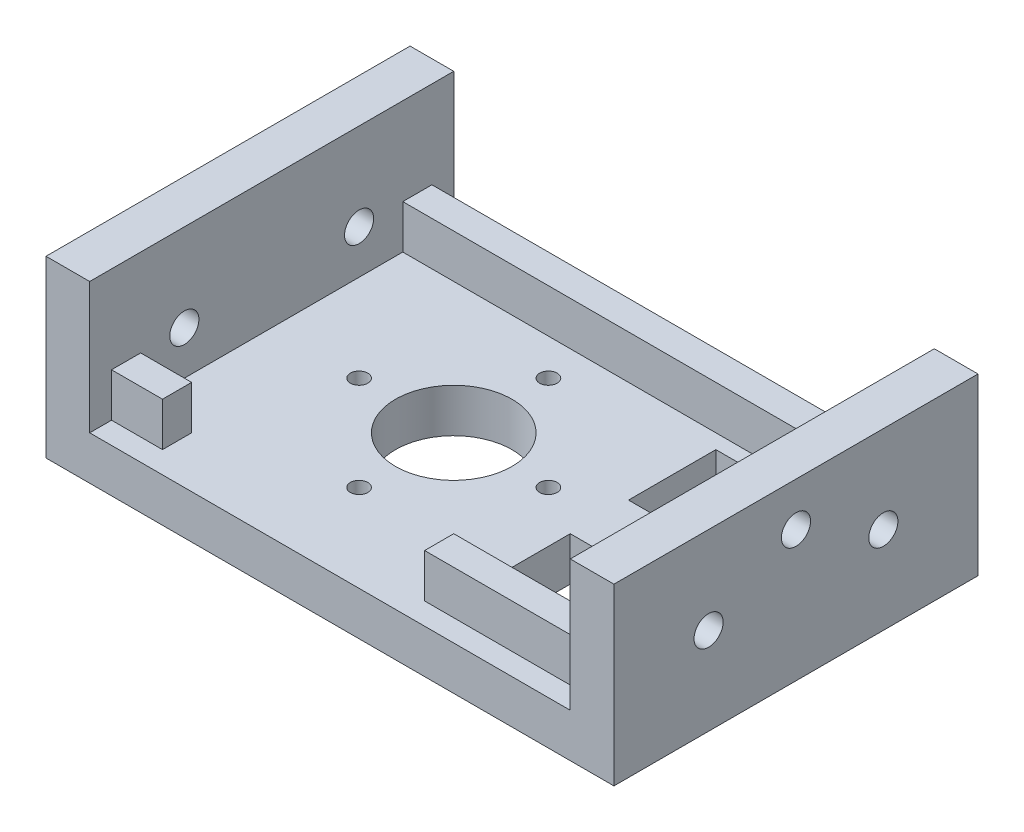
SolidWorks part; units mm, degrees
ref_plane "Alzado" through (0, 0, 0) normal (0, 0, 1) x (1, 0, 0)
ref_plane "Planta" through (0, 0, 0) normal (0, 1, 0) x (1, 0, 0)
ref_plane "Vista lateral" through (0, 0, 0) normal (1, 0, 0) x (0, 0, -1)
sketch "Croquis1" plane through (0, 0, 0) normal (0, 1, 0) x (1, 0, 0)
  line L0 (-18.5924, 13.748) -> (20.4076, 13.748)
  line L1 (-18.5924, 13.748) -> (-18.5924, -11.252)
  line L2 (-18.5924, -11.252) -> (20.4076, -11.252)
  line L3 (20.4076, 13.748) -> (20.4076, -11.252)
  line L4 (6.9076, -0.752) -> (14.9076, -0.752)
  line L5 (6.9076, -0.752) -> (6.9076, -6.752)
  line L6 (6.9076, -6.752) -> (14.9076, -6.752)
  line L7 (14.9076, -0.752) -> (14.9076, -6.752)
  line L8 (6.9076, 9.248) -> (14.9076, 9.248)
  line L9 (6.9076, 9.248) -> (6.9076, 3.248)
  line L10 (6.9076, 3.248) -> (14.9076, 3.248)
  line L11 (14.9076, 9.248) -> (14.9076, 3.248)
  circle A0 centre (-3.0924, 1.248) radius 4
  circle A1 centre (-3.0924, 7.748) radius 0.6
  circle A2 centre (3.4076, 1.248) radius 0.6
  circle A3 centre (-3.0924, -5.252) radius 0.6
  circle A4 centre (-9.5924, 1.248) radius 0.6
  point P22 (-3.0924, 1.248)
extrude "Saliente-Extruir1" add sketch "Croquis1" along normal blind 3
sketch "Croquis2" plane through (0, 3, 0) normal (0, 1, 0) x (1, 0, 0)
  line L0 (-18.5924, -11.252) -> (20.4076, -11.252) construction
  line L1 (-18.5924, 13.748) -> (-15.5924, 13.748)
  line L2 (-18.5924, 13.748) -> (-18.5924, -11.252)
  line L3 (-18.5924, -11.252) -> (-15.5924, -11.252)
  line L4 (-15.5924, 13.748) -> (-15.5924, 12.248)
  line L5 (20.4076, 13.748) -> (-18.5924, 13.748) construction
  line L6 (17.4076, 13.748) -> (20.4076, 13.748)
  line L7 (17.4076, 13.748) -> (17.4076, 12.248)
  line L8 (17.4076, -11.252) -> (20.4076, -11.252)
  line L9 (20.4076, 13.748) -> (20.4076, -11.252)
  line L10 (5.9076, -9.752) -> (17.4076, -9.752)
  line L11 (-15.5924, -7.752) -> (-12.0924, -7.752)
  line L13 (-15.5924, -9.752) -> (-12.0924, -9.752)
  line L16 (-12.0924, -7.752) -> (-12.0924, -9.752)
  line L18 (5.9076, -7.752) -> (5.9076, -9.752)
  line L19 (-15.5924, 12.248) -> (17.4076, 12.248)
  line L21 (-15.5924, 10.248) -> (17.4076, 10.248)
  line L23 (5.9076, -7.752) -> (17.4076, -7.752)
  line L24 (-15.5924, -9.752) -> (-15.5924, -11.252)
  line L25 (17.4076, -9.752) -> (17.4076, -11.252)
  line L26 (-15.5924, 10.248) -> (-15.5924, -7.752)
  line L27 (17.4076, 10.248) -> (17.4076, -7.752)
  dimension "D1" = 33
  dimension "D2" = 3.5
  dimension "D3" = 11.5
  dimension "D4" = 2
  dimension "D5" = 1.5
  dimension "D6" = 1.5
  dimension "D7" = 2
extrude "Saliente-Extruir2" add sketch "Croquis2" along normal blind 3
sketch "Croquis3" plane through (0, 6, 0) normal (0, 1, 0) x (1, 0, 0)
  line L1 (-18.5924, 13.748) -> (-15.5924, 13.748)
  line L2 (-18.5924, 13.748) -> (-18.5924, -11.252)
  line L3 (-18.5924, -11.252) -> (-15.5924, -11.252)
  line L4 (-15.5924, 13.748) -> (-15.5924, -11.252)
  line L5 (20.4076, -11.252) -> (17.4076, -11.252)
  line L6 (20.4076, -11.252) -> (20.4076, 13.748)
  line L7 (20.4076, 13.748) -> (17.4076, 13.748)
  line L8 (17.4076, -11.252) -> (17.4076, 13.748)
extrude "Saliente-Extruir3" add sketch "Croquis3" along normal blind 6
sketch "Croquis4" plane through (-18.5924, 0, 0) normal (-1, 0, 0) x (0, 0, 1)
  line L0 (-13.748, 12) -> (-13.748, 0) construction
  line L1 (-13.748, 0) -> (11.252, 0) construction
  circle A0 centre (-7.248, 6) radius 1
  circle A1 centre (4.752, 6) radius 1
  point P4 (0, 0)
  dimension "D1" = 2
  dimension "D2" = 6.5
  dimension "D3" = 12
  dimension "D4" = 6
extrude "Cortar-Extruir1" cut sketch "Croquis4" against normal blind 45
sketch "Croquis5" plane through (20.4076, 0, 0) normal (1, 0, 0) x (0, 0, -1)
  circle A0 centre (1.248, 9) radius 1
  circle A1 centre (-4.752, 6) radius 1 construction
  dimension "D2" = 2
  dimension "D1" = 6
  dimension "D3" = 3
extrude "Cortar-Extruir2" cut sketch "Croquis5" against normal blind 27
